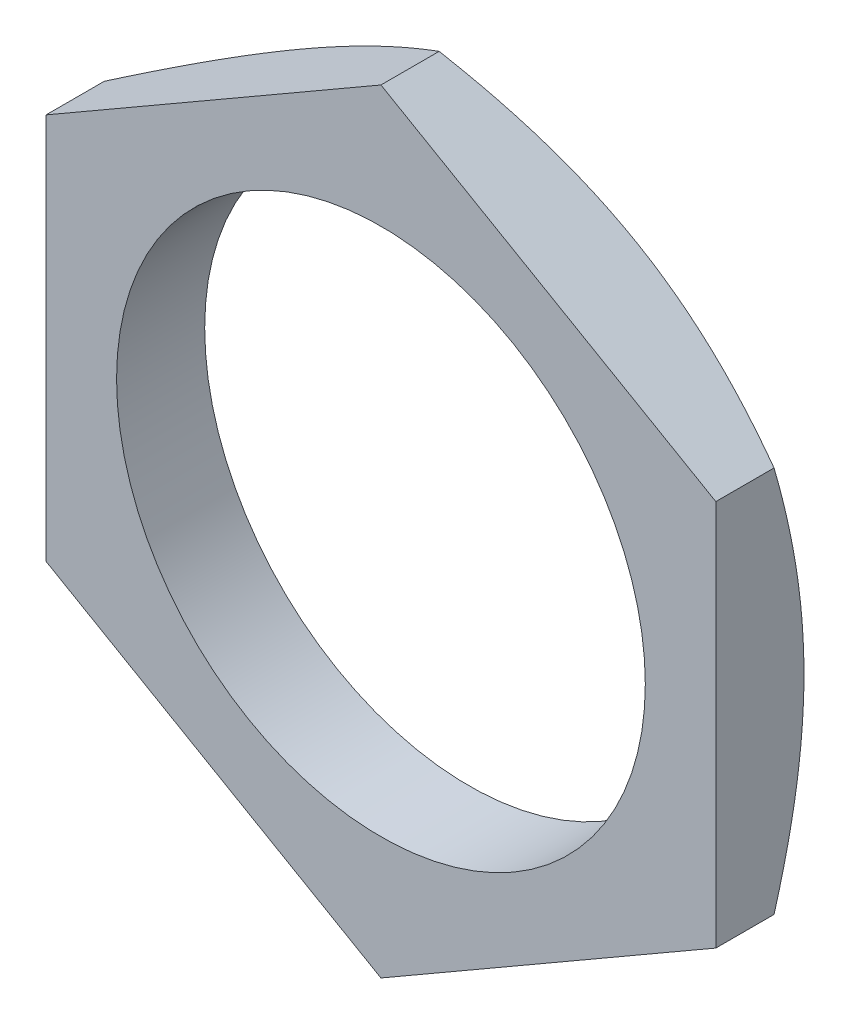
SolidWorks part; units mm, degrees
material "1023 Carbon Steel Sheet (SS)"
ref_plane "Front Plane" through (0, 0, 0) normal (0, 0, 1) x (1, 0, 0)
ref_plane "Top Plane" through (0, 0, 0) normal (0, 1, 0) x (1, 0, 0)
ref_plane "Right Plane" through (0, 0, 0) normal (1, 0, 0) x (0, 0, -1)
sketch "Sketch1" plane through (0, 0, 0) normal (0, 0, 1) x (1, 0, 0)
  line L1 (0, 10.9697) -> (-9.5, 5.4848)
  line L2 (-9.5, 5.4848) -> (-9.5, -5.4848)
  line L3 (-9.5, -5.4848) -> (0, -10.9697)
  line L4 (0, -10.9697) -> (9.5, -5.4848)
  line L5 (9.5, -5.4848) -> (9.5, 5.4848)
  line L6 (9.5, 5.4848) -> (0, 10.9697)
  circle A0 centre (0, 0) radius 9.5 construction
  circle A1 centre (0, 0) radius 7.5
  dimension "D2" = 15
  dimension "D1" = 19
extrude "Boss-Extrude1" add sketch "Sketch1" along normal mid plane 2.5
sketch "Sketch2" plane through (0, 0, 0) normal (0, 1, 0) x (1, 0, 0)
  line L0 (-9.5, 1.25) -> (-12.9775, -0.7578)
  line L1 (-12.9775, -0.7578) -> (-12.9775, 1.25)
  line L2 (-12.9775, 1.25) -> (-9.5, 1.25)
  line L3 (0, 0) -> (0, 2.9841) construction
  line L4 (0, -1.25) -> (0, 1.25) construction
  dimension "D1" = 30
revolve "Cut-Revolve1" cut sketch "Sketch2" angle 360 about L3
